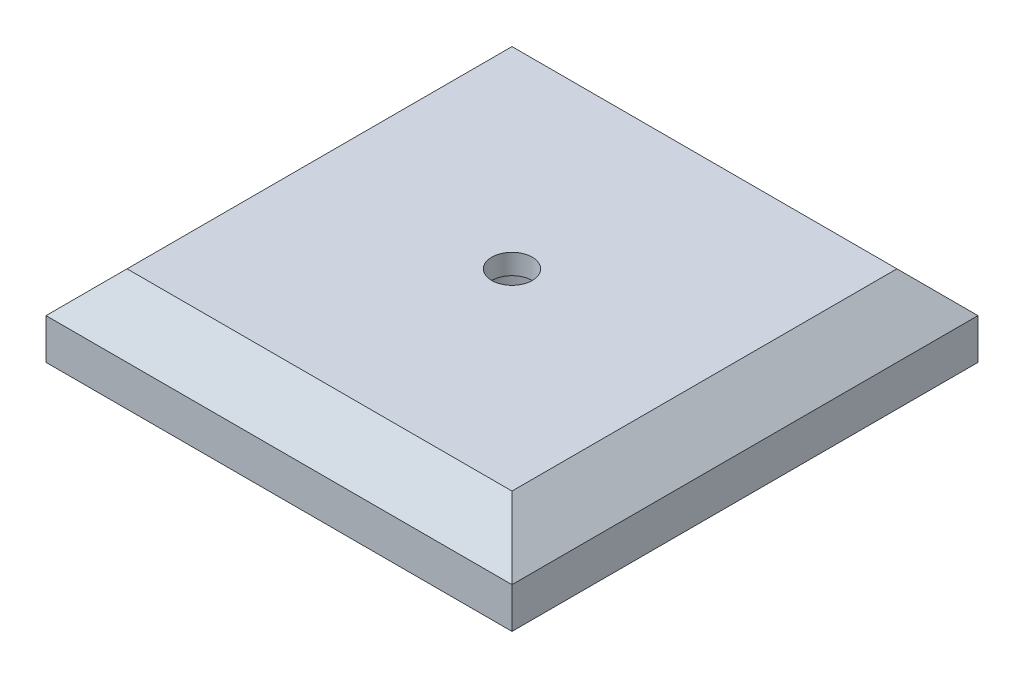
SolidWorks part; units mm, degrees
material "Plain Carbon Steel"
ref_plane "Front Plane" through (0, 0, 0) normal (0, 0, 1) x (1, 0, 0)
ref_plane "Top Plane" through (0, 0, 0) normal (0, 1, 0) x (1, 0, 0)
ref_plane "Right Plane" through (0, 0, 0) normal (1, 0, 0) x (0, 0, -1)
sketch "Sketch1" plane through (0, 0, 0) normal (0, 1, 0) x (1, 0, 0)
  line L1 (-36.5125, -36.5125) -> (36.5125, -36.5125)
  line L2 (-36.5125, -36.5125) -> (-36.5125, 36.5125)
  line L3 (-36.5125, 36.5125) -> (36.5125, 36.5125)
  line L4 (36.5125, -36.5125) -> (36.5125, 36.5125)
  line L5 (-36.5125, -36.5125) -> (36.5125, 36.5125) construction
  line L6 (-36.5125, 36.5125) -> (36.5125, -36.5125) construction
  point P0 (0, 0)
  dimension "D1" = 73.025
extrude "Boss-Extrude1" add sketch "Sketch1" along normal blind 12.7
chamfer "Chamfer1" distance 6.35 angle 45 4 edges at (-36.5125, 12.7, 0) (0, 12.7, -36.5125) (36.5125, 12.7, 0) (0, 12.7, 36.5125)
sketch "Sketch2" plane through (0, 12.7, 0) normal (0, 1, 0) x (1, 0, 0)
  circle A0 centre (0, 0) radius 3.175
  dimension "D1" = 6.35
extrude "Cut-Extrude1" cut sketch "Sketch2" against normal blind 3.175
sketch "Sketch3" plane through (0, 0, 0) normal (0, -1, 0) x (1, 0, 0)
  circle A0 centre (0, 0) radius 6.35
  dimension "D1" = 12.7
extrude "Cut-Extrude2" cut sketch "Sketch3" against normal up to surface (9.525 mm away) up to face at (0, 9.525, 3.175)
